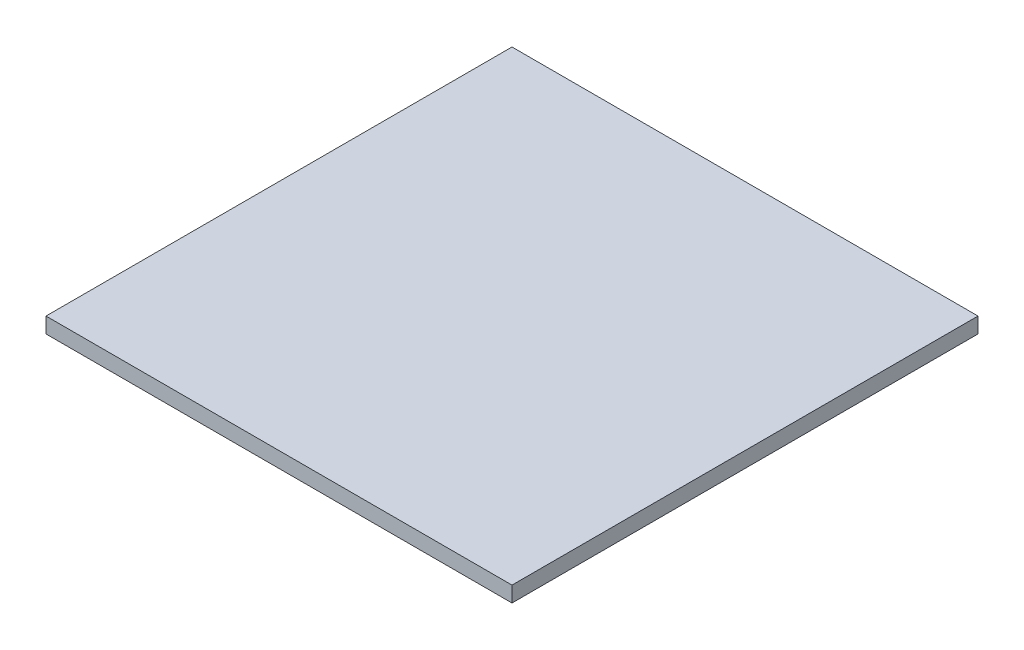
SolidWorks part; units mm, degrees
material "Oak"
ref_plane "Front Plane" through (0, 0, 0) normal (0, 0, 1) x (1, 0, 0)
ref_plane "Top Plane" through (0, 0, 0) normal (0, 1, 0) x (1, 0, 0)
ref_plane "Right Plane" through (0, 0, 0) normal (1, 0, 0) x (0, 0, -1)
sketch "Sketch2" plane through (0, 0, 0) normal (0, 1, 0) x (1, 0, 0)
  line L1 (-1500, -1500) -> (1500, -1500)
  line L2 (-1500, -1500) -> (-1500, 1500)
  line L3 (-1500, 1500) -> (1500, 1500)
  line L4 (1500, -1500) -> (1500, 1500)
  line L5 (-1500, -1500) -> (1500, 1500) construction
  line L6 (-1500, 1500) -> (1500, -1500) construction
  point P0 (0, 0)
  dimension "D1" = 3000
  dimension "D2" = 3000
extrude "Boss-Extrude1" add sketch "Sketch2" along normal blind 100
